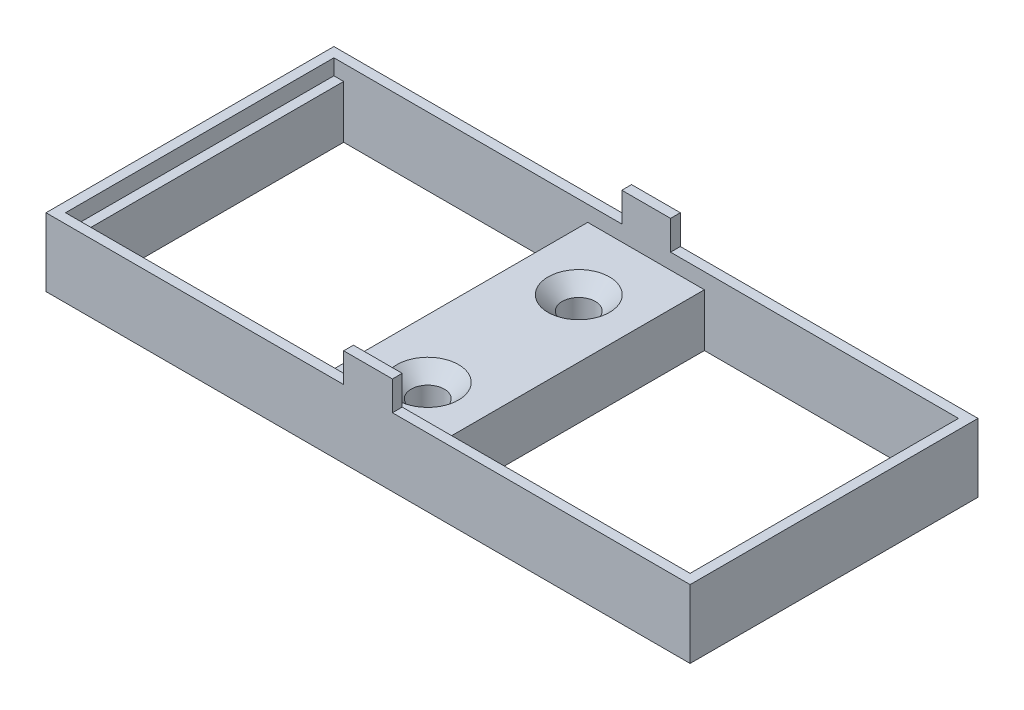
SolidWorks part; units mm, degrees
ref_plane "Front Plane" through (0, 0, 0) normal (0, 0, 1) x (1, 0, 0)
ref_plane "Top Plane" through (0, 0, 0) normal (0, 1, 0) x (1, 0, 0)
ref_plane "Right Plane" through (0, 0, 0) normal (1, 0, 0) x (0, 0, -1)
sketch "Sketch1" plane through (0, 0, 0) normal (0, 1, 0) x (1, 0, 0)
  line L1 (0, 0) -> (66, 0)
  line L2 (0, 0) -> (0, -29.5)
  line L3 (0, -29.5) -> (66, -29.5)
  line L4 (66, 0) -> (66, -29.5)
extrude "Boss-Extrude1" add sketch "Sketch1" along normal blind 7 contours L2 L1 L4 L3
sketch "Sketch2" plane through (0, 7, 0) normal (0, 1, 0) x (1, 0, 0)
  line L0 (0, 0) -> (66, 0) construction
  line L1 (1, -1) -> (65, -1)
  line L2 (1, -1) -> (1, -28.5)
  line L3 (1, -28.5) -> (65, -28.5)
  line L4 (65, -1) -> (65, -28.5)
  line L5 (0, -29.5) -> (66, -29.5) construction
  line L6 (0, 0) -> (0, -29.5) construction
  line L7 (66, 0) -> (66, -29.5) construction
  dimension "D1" = 1
  dimension "D2" = 1
  dimension "D3" = 1
  dimension "D4" = 1
sketch "Sketch4" plane through (0, 0.9, 0) normal (0, 1, 0) x (1, 0, 0)
  line L1 (65, -1) -> (1, -1) construction
  line L6 (2, -1) -> (27.0089, -1)
  line L7 (2, -1) -> (2, -28.5)
  line L8 (2, -28.5) -> (27.0089, -28.5)
  line L9 (27.0089, -1) -> (27.0089, -28.5)
  line L10 (1, -28.5) -> (65, -28.5) construction
  line L11 (1, -1) -> (1, -28.5) construction
  line L12 (65, -28.5) -> (65, -1) construction
  line L13 (64, -1) -> (38.9664, -1)
  line L14 (64, -1) -> (64, -28.5)
  line L15 (64, -28.5) -> (38.9664, -28.5)
  line L16 (38.9664, -1) -> (38.9664, -28.5)
  dimension "D1" = 1
  dimension "D2" = 1
sketch "Sketch5" plane through (0, 0.9, 0) normal (0, 1, 0) x (1, 0, 0)
  line L0 (19, -1) -> (47, -28.5)
  line L1 (47, -1) -> (19, -28.5)
sketch "Sketch18" plane through (0, 7, 0) normal (0, 1, 0) x (1, 0, 0)
  line L0 (0, 0) -> (66, 0) construction
  line L1 (30.5, 0) -> (35.5, 0)
  line L2 (30.5, 0) -> (30.5, -1)
  line L3 (30.5, -1) -> (35.5, -1)
  line L4 (35.5, 0) -> (35.5, -1)
  line L5 (65, -1) -> (1, -1) construction
  line L6 (1, -28.5) -> (65, -28.5) construction
  line L7 (35.5, -28.5) -> (30.5, -28.5)
  line L8 (35.5, -28.5) -> (35.5, -29.5)
  line L9 (35.5, -29.5) -> (30.5, -29.5)
  line L10 (30.5, -28.5) -> (30.5, -29.5)
  line L11 (0, -29.5) -> (66, -29.5) construction
  line L13 (0, 0) -> (0, -29.5) construction
  line L14 (66, 0) -> (66, -29.5) construction
  dimension "D2" = 30.5
  dimension "D3" = 30.5
extrude "Boss-Extrude3" add sketch "Sketch18" along normal blind 3
extrude "Cut-Extrude1" cut sketch "Sketch2" against normal blind 1.6
sketch "Sketch19" plane through (0, 5.4, 0) normal (0, 1, 0) x (1, 0, 0)
  line L1 (2, -1) -> (27.0089, -1)
  line L2 (2, -1) -> (2, -28.5)
  line L3 (2, -28.5) -> (27.0089, -28.5)
  line L4 (27.0089, -1) -> (27.0089, -28.5)
  line L5 (38.9664, -1) -> (64, -1)
  line L6 (38.9664, -1) -> (38.9664, -28.5)
  line L7 (38.9664, -28.5) -> (64, -28.5)
  line L8 (64, -1) -> (64, -28.5)
extrude "Cut-Extrude3" cut sketch "Sketch19" against normal blind 10
hole_wizard "CSK for M3 Countersunk Flat Head Screw2" positions "3DSketch3" profile "Sketch22" countersink size "M3" standard "ISO" end condition through all
sketch3d "3DSketch3"
  line L0 (35.5, 10, 28.5) -> (30.5, 10, 28.5) construction
  line L1 (38.9664, 5.4, 1) -> (27.0089, 5.4, 1) construction
  line L2 (38.9664, 5.4, 1) -> (38.9664, 5.4, 28.5) construction
  line L3 (27.0089, 5.4, 28.5) -> (27.0089, 5.4, 1) construction
  point P0 (32.9664, 5.4, 7.875)
  point P2 (33.0089, 5.4, 23.3906)
  dimension "D1" = 6.875
  dimension "D2" = 6.875
  dimension "D3" = 6
  dimension "D4" = 6
sketch "Sketch22" plane through (32.9664, 5.4, 7.875) normal (1, 0, 0) x (0, 0, 1)
  line L0 (0, 0) -> (0, 5.4)
  line L1 (0, 5.4) -> (1.7, 5.4)
  line L2 (1.7, 5.4) -> (1.7, 1.45)
  line L3 (1.7, 1.45) -> (3.15, 0)
  line L5 (3.15, 0) -> (0, 0)
  line L6 (-1.7, 1.45) -> (-3.15, 0) construction
  line L11 (0, -6.35) -> (0, 107.95) construction
  dimension "Thru Hole Dia." = 3.4
  dimension "Thru Hole Depth" = 5.4
  dimension "Near C'Sink Dia." = 6.3
  dimension "Near C'Sink Angle" = 90
